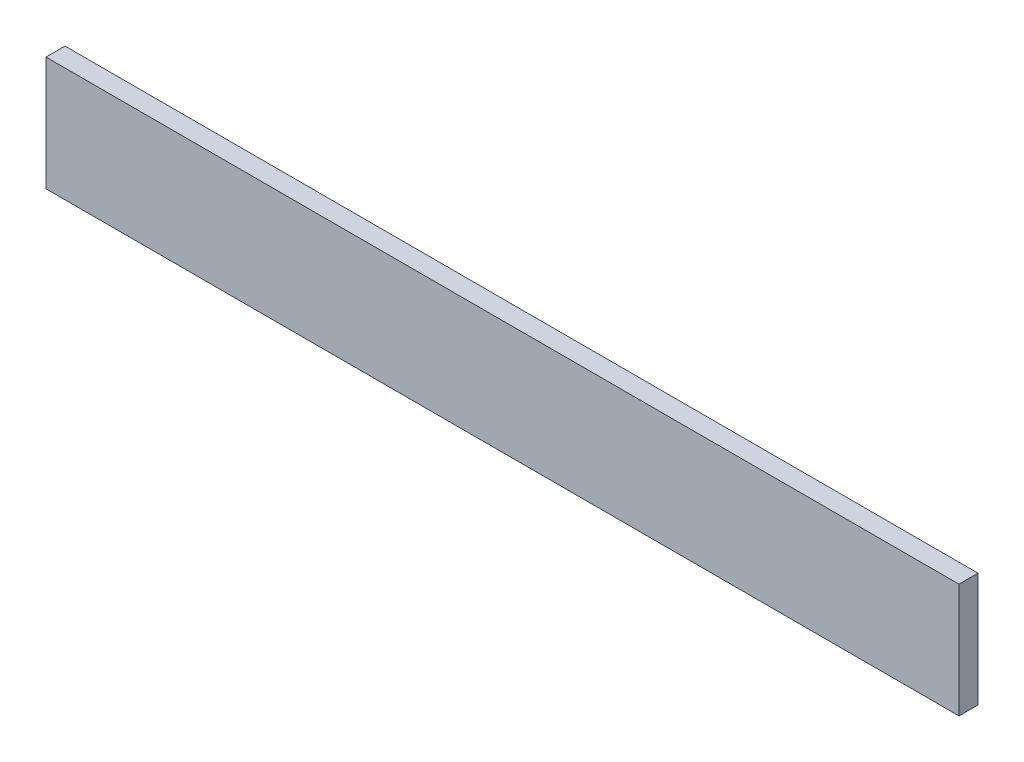
SolidWorks part; units mm, degrees
ref_plane "Front Plane" through (0, 0, 0) normal (0, 0, 1) x (1, 0, 0)
ref_plane "Top Plane" through (0, 0, 0) normal (0, 1, 0) x (1, 0, 0)
ref_plane "Right Plane" through (0, 0, 0) normal (1, 0, 0) x (0, 0, -1)
sketch "Sketch1" plane through (0, 0, 0) normal (0, 0, 1) x (1, 0, 0)
  line L1 (0, 0) -> (304.8, 0)
  line L2 (0, 0) -> (0, 38.1)
  line L3 (0, 38.1) -> (304.8, 38.1)
  line L4 (304.8, 0) -> (304.8, 38.1)
  dimension "D1" = 38.1
  dimension "D2" = 304.8
extrude "Boss-Extrude1" add sketch "Sketch1" along normal blind 6.35
